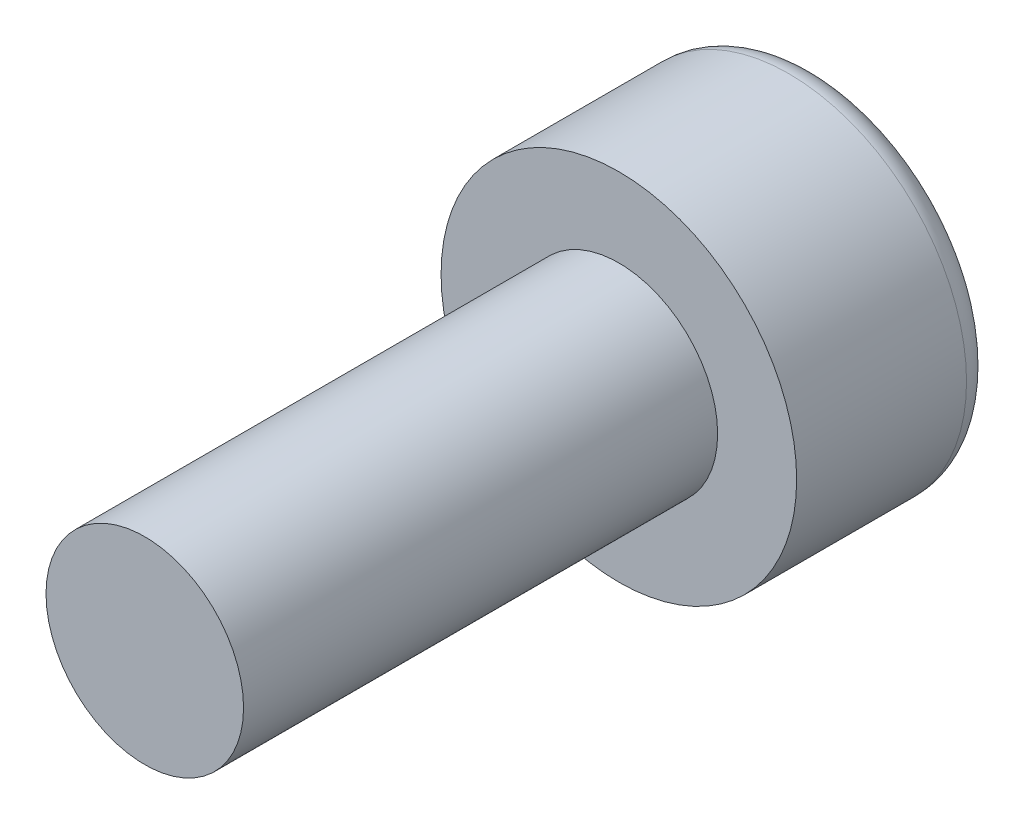
SolidWorks part; units mm, degrees
material "Acero aleado"
ref_plane "Alzado" through (0, 0, 0) normal (0, 0, 1) x (1, 0, 0)
ref_plane "Planta" through (0, 0, 0) normal (0, 1, 0) x (1, 0, 0)
ref_plane "Vista lateral" through (0, 0, 0) normal (1, 0, 0) x (0, 0, -1)
sketch "Croquis1" plane through (0, 0, 0) normal (0, 0, 1) x (1, 0, 0)
  circle A0 centre (0, 0) radius 1.25
  dimension "D1" = 2.5
extrude "Saliente-Extruir1" add sketch "Croquis1" along normal blind 6
sketch "Croquis2" plane through (0, 0, 0) normal (0, 0, -1) x (-1, 0, 0)
  circle A0 centre (0, 0) radius 2.25
  dimension "D1" = 4.5
extrude "Saliente-Extruir2" add sketch "Croquis2" along normal blind 2.5
sketch "Croquis3" plane through (0, 0, -2.5) normal (0, 0, -1) x (-1, 0, 0)
  line L1 (0, -1.1547) -> (1, -0.5774)
  line L2 (1, -0.5774) -> (1, 0.5774)
  line L3 (1, 0.5774) -> (0, 1.1547)
  line L4 (0, 1.1547) -> (-1, 0.5774)
  line L5 (-1, 0.5774) -> (-1, -0.5774)
  line L6 (-1, -0.5774) -> (0, -1.1547)
  circle A0 centre (0, 0) radius 1 construction
  dimension "D1" = 2
extrude "Cortar-Extruir1" cut sketch "Croquis3" against normal blind 1.5
fillet "Redondeo1" radius 0.35 1 edges at (-2.25, 0, -2.5)
